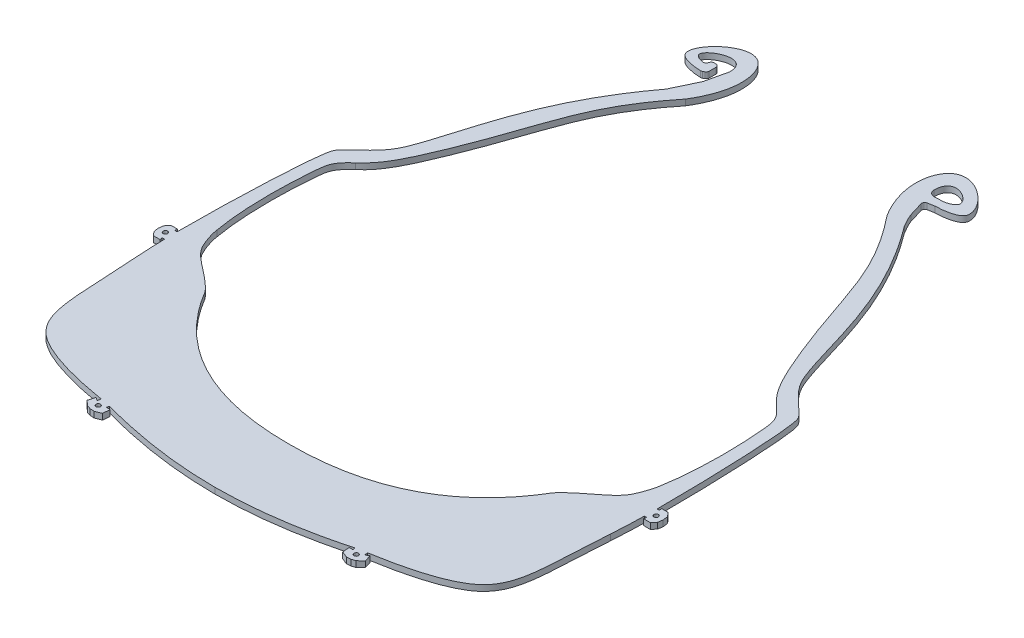
SolidWorks part; units mm, degrees
ref_plane "Front Plane" through (0, 0, 0) normal (0, 0, 1) x (1, 0, 0)
ref_plane "Top Plane" through (0, 0, 0) normal (0, 1, 0) x (1, 0, 0)
ref_plane "Right Plane" through (0, 0, 0) normal (1, 0, 0) x (0, 0, -1)
sketch "Sketch1" plane through (0, 0, 0) normal (0, 1, 0) x (1, 0, 0)
  line L0 (-56.7342, 4649.685) -> (-54.3432, 4649.8666)
  line L1 (-54.3432, 4649.8666) -> (-51.9673, 4650.1279)
  line L2 (-51.9673, 4650.1279) -> (-49.6128, 4650.4904)
  line L3 (-49.6128, 4650.4904) -> (-47.2873, 4650.9763)
  line L4 (-47.2873, 4650.9763) -> (-45.0028, 4651.606)
  line L5 (-45.0028, 4651.606) -> (-42.7754, 4652.393)
  line L6 (-42.7754, 4652.393) -> (-40.6236, 4653.3398)
  line L7 (-40.6236, 4653.3398) -> (-38.5569, 4654.4471)
  line L8 (-38.5569, 4654.4471) -> (-36.5628, 4655.7048)
  line L9 (-36.5628, 4655.7048) -> (-34.628, 4657.0886)
  line L10 (-34.628, 4657.0886) -> (-32.7572, 4658.5809)
  line L11 (-32.7572, 4658.5809) -> (-31.8781, 4659.3559)
  line L12 (-31.8781, 4659.3559) -> (-31.0378, 4660.1663)
  line L13 (-31.0378, 4660.1663) -> (-30.2434, 4661.0133)
  line L14 (-30.2434, 4661.0133) -> (-29.4929, 4661.8977)
  line L15 (-29.4929, 4661.8977) -> (-28.0377, 4663.8002)
  line L16 (-28.0377, 4663.8002) -> (-26.6418, 4665.7643)
  line L17 (-26.6418, 4665.7643) -> (-25.2842, 4667.7433)
  line L18 (-25.2842, 4667.7433) -> (-24.5616, 4668.7671)
  line L19 (-24.5616, 4668.7671) -> (-24.1207, 4669.3049)
  line L20 (-24.1207, 4669.3049) -> (-23.6287, 4669.8041)
  line L21 (-23.6287, 4669.8041) -> (-22.6527, 4670.6453)
  line L22 (-22.6527, 4670.6453) -> (-21.6624, 4671.4168)
  line L23 (-21.6624, 4671.4168) -> (-19.7154, 4672.8766)
  line L24 (-19.7154, 4672.8766) -> (-18.7888, 4673.6051)
  line L25 (-18.7888, 4673.6051) -> (-17.9151, 4674.3646)
  line L26 (-17.9151, 4674.3646) -> (-17.0961, 4675.1711)
  line L27 (-17.0961, 4675.1711) -> (-16.3332, 4676.0235)
  line L28 (-16.3332, 4676.0235) -> (-14.888, 4677.8872)
  line L29 (-14.888, 4677.8872) -> (-14.2651, 4678.8282)
  line L30 (-14.2651, 4678.8282) -> (-13.7395, 4679.8092)
  line L31 (-13.7395, 4679.8092) -> (-13.3157, 4680.8364)
  line L32 (-13.3157, 4680.8364) -> (-12.9921, 4681.9053)
  line L33 (-12.9921, 4681.9053) -> (-12.765, 4683.0137)
  line L34 (-12.765, 4683.0137) -> (-12.6116, 4684.156)
  line L35 (-12.6116, 4684.156) -> (-12.4221, 4686.5439)
  line L36 (-12.4221, 4686.5439) -> (-12.3049, 4688.9547)
  line L37 (-12.3049, 4688.9547) -> (-12.23, 4691.3606)
  line L38 (-12.23, 4691.3606) -> (-12.2173, 4693.7469)
  line L39 (-12.2173, 4693.7469) -> (-12.2979, 4696.128)
  line L40 (-12.2979, 4696.128) -> (-12.4621, 4698.525)
  line L41 (-12.4621, 4698.525) -> (-12.9016, 4703.3562)
  line L42 (-12.9016, 4703.3562) -> (-13.1725, 4705.7323)
  line L43 (-13.1725, 4705.7323) -> (-13.359, 4706.8497)
  line L44 (-13.359, 4706.8497) -> (-13.6464, 4707.8976)
  line L45 (-13.6464, 4707.8976) -> (-13.8331, 4708.3435)
  line L46 (-13.8331, 4708.3435) -> (-14.0727, 4708.7863)
  line L47 (-14.0727, 4708.7863) -> (-14.3603, 4709.2104)
  line L48 (-14.3603, 4709.2104) -> (-14.6922, 4709.6118)
  line L49 (-14.6922, 4709.6118) -> (-15.5352, 4710.4427)
  line L50 (-15.5352, 4710.4427) -> (-16.4733, 4711.2489)
  line L51 (-16.4733, 4711.2489) -> (-18.3969, 4712.8768)
  line L52 (-18.3969, 4712.8768) -> (-19.3317, 4713.7593)
  line L53 (-19.3317, 4713.7593) -> (-19.7964, 4714.2738)
  line L54 (-19.7964, 4714.2738) -> (-20.226, 4714.8564)
  line L55 (-20.226, 4714.8564) -> (-20.8491, 4716.0227)
  line L56 (-20.8491, 4716.0227) -> (-21.3607, 4717.2182)
  line L57 (-21.3607, 4717.2182) -> (-22.2565, 4719.6128)
  line L58 (-22.2565, 4719.6128) -> (-23.9365, 4724.4003)
  line L59 (-23.9365, 4724.4003) -> (-24.8142, 4726.6925)
  line L60 (-24.8142, 4726.6925) -> (-25.7235, 4728.951)
  line L61 (-25.7235, 4728.951) -> (-29.4192, 4737.978)
  line L62 (-29.4192, 4737.978) -> (-31.3112, 4742.476)
  line L63 (-31.3112, 4742.476) -> (-32.3108, 4744.6883)
  line L64 (-32.3108, 4744.6883) -> (-33.3653, 4746.8748)
  line L65 (-33.3653, 4746.8748) -> (-34.484, 4749.0197)
  line L66 (-34.484, 4749.0197) -> (-35.6822, 4751.1089)
  line L67 (-35.6822, 4751.1089) -> (-36.9697, 4753.1376)
  line L68 (-36.9697, 4753.1376) -> (-38.335, 4755.1176)
  line L69 (-38.335, 4755.1176) -> (-39.7566, 4757.0561)
  line L70 (-39.7566, 4757.0561) -> (-41.2239, 4758.9538)
  line L71 (-41.2239, 4758.9538) -> (-44.2837, 4762.6862)
  line L72 (-44.2837, 4762.6862) -> (-45.0093, 4763.5782)
  line L73 (-45.7102, 4766.0333) -> (-45.6003, 4766.895)
  line L74 (-44.3387, 4767.2717) -> (-41.5099, 4763.9631)
  line L75 (-41.5099, 4763.9631) -> (-39.7615, 4761.7893)
  line L76 (-39.7615, 4761.7893) -> (-36.1552, 4757.1077)
  line L77 (-36.1552, 4757.1077) -> (-34.4224, 4754.6956)
  line L78 (-34.4224, 4754.6956) -> (-32.818, 4752.1875)
  line L79 (-32.818, 4752.1875) -> (-31.4001, 4749.5854)
  line L80 (-31.4001, 4749.5854) -> (-30.1172, 4746.945)
  line L81 (-30.1172, 4746.945) -> (-27.7453, 4741.6402)
  line L82 (-27.7453, 4741.6402) -> (-25.4835, 4736.2816)
  line L83 (-25.4835, 4736.2816) -> (-23.2904, 4730.8724)
  line L84 (-23.2904, 4730.8724) -> (-21.1708, 4725.4153)
  line L85 (-21.1708, 4725.4153) -> (-19.1018, 4719.943)
  line L86 (-19.1018, 4719.943) -> (-18.1004, 4717.2034)
  line L87 (-18.1004, 4717.2034) -> (-17.875, 4716.5966)
  line L88 (-17.875, 4716.5966) -> (-17.6236, 4716.1359)
  line L89 (-17.6236, 4716.1359) -> (-17.2675, 4715.7336)
  line L90 (-17.2675, 4715.7336) -> (-16.7845, 4715.2999)
  line L91 (-16.7845, 4715.2999) -> (-14.566, 4713.4273)
  line L92 (-14.566, 4713.4273) -> (-13.4359, 4712.453)
  line L93 (-13.4359, 4712.453) -> (-12.2875, 4711.3506)
  line L94 (-12.2875, 4711.3506) -> (-11.7288, 4710.5494)
  line L95 (-11.7288, 4710.5494) -> (-11.4049, 4709.6505)
  line L96 (-11.4049, 4709.6505) -> (-11.1035, 4708.0976)
  line L97 (-11.1035, 4708.0976) -> (-10.7039, 4705.1867)
  line L98 (-10.7039, 4705.1867) -> (-10.3782, 4702.2301)
  line L99 (-10.3782, 4702.2301) -> (-10.1381, 4699.312)
  line L100 (-10.1381, 4699.312) -> (-9.9526, 4696.4059)
  line L101 (-9.9526, 4696.4059) -> (-9.8234, 4693.4642)
  line L102 (-9.8234, 4693.4642) -> (-9.7818, 4690.5097)
  line L103 (-9.7818, 4690.5097) -> (-9.8395, 4687.5651)
  line L104 (-9.8395, 4687.5651) -> (-10.1467, 4681.8499)
  line L105 (-10.2187, 4680.4106) -> (-10.5778, 4674.8324)
  line L106 (-10.5778, 4674.8324) -> (-10.9255, 4669.1921)
  line L107 (-10.9255, 4669.1921) -> (-11.1085, 4666.3239)
  line L108 (-11.1085, 4666.3239) -> (-11.3672, 4663.3976)
  line L109 (-11.3672, 4663.3976) -> (-11.5954, 4661.8877)
  line L110 (-11.5954, 4661.8877) -> (-11.9481, 4660.3817)
  line L111 (-11.9481, 4660.3817) -> (-12.469, 4658.9063)
  line L112 (-12.469, 4658.9063) -> (-13.1768, 4657.5086)
  line L113 (-13.1768, 4657.5086) -> (-14.0475, 4656.2056)
  line L114 (-14.0475, 4656.2056) -> (-15.0678, 4655.0233)
  line L115 (-15.0678, 4655.0233) -> (-15.6664, 4654.4674)
  line L116 (-15.6664, 4654.4674) -> (-16.3022, 4653.9611)
  line L117 (-16.3022, 4653.9611) -> (-17.6055, 4653.1269)
  line L118 (-17.6055, 4653.1269) -> (-18.9712, 4652.4383)
  line L119 (-18.9712, 4652.4383) -> (-20.3502, 4651.8561)
  line L120 (-20.3502, 4651.8561) -> (-21.7405, 4651.3486)
  line L121 (-21.7405, 4651.3486) -> (-23.1491, 4650.8937)
  line L122 (-23.1491, 4650.8937) -> (-25.9685, 4650.1281)
  line L123 (-25.9685, 4650.1281) -> (-28.8127, 4649.495)
  line L124 (-28.8127, 4649.495) -> (-34.3611, 4648.4388)
  line L125 (-35.7786, 4648.1905) -> (-42.1243, 4647.1501)
  line L126 (-42.1243, 4647.1501) -> (-45.3893, 4646.7207)
  line L127 (-45.3893, 4646.7207) -> (-48.6635, 4646.3827)
  line L128 (-48.6635, 4646.3827) -> (-55.1892, 4645.922)
  line L129 (-55.1892, 4645.922) -> (-61.7354, 4645.5886)
  line L130 (-61.7354, 4645.5886) -> (-63.9666, 4645.5453)
  line L131 (-63.9667, 4649.4865) -> (-59.1315, 4649.5688)
  line L132 (-59.1315, 4649.5688) -> (-56.7342, 4649.685)
  line L133 (-9.7721, 4681.8294) -> (-9.752, 4682.186)
  line L134 (-9.752, 4682.186) -> (-9.3693, 4682.5229)
  line L135 (-9.3693, 4682.5229) -> (-8.649, 4682.4768)
  line L136 (-8.649, 4682.4768) -> (-7.9775, 4681.713)
  line L137 (-7.9775, 4681.713) -> (-8.2411, 4680.2884)
  line L138 (-8.2411, 4680.2884) -> (-9.0059, 4679.6162)
  line L139 (-9.0059, 4679.6162) -> (-9.5491, 4679.6473)
  line L140 (-9.5491, 4679.6473) -> (-9.8867, 4680.0303)
  line L141 (-9.8867, 4680.0303) -> (-9.8664, 4680.3889)
  line L142 (-9.7721, 4681.8294) -> (-9.752, 4682.186)
  line L151 (-34.2991, 4648.0806) -> (-33.9447, 4648.1421)
  line L152 (-33.9447, 4648.1421) -> (-33.5285, 4647.8485)
  line L153 (-33.5285, 4647.8485) -> (-33.4056, 4647.1395)
  line L154 (-33.4056, 4647.1395) -> (-33.9931, 4646.3074)
  line L155 (-33.9931, 4646.3074) -> (-35.4108, 4646.0612)
  line L156 (-35.4108, 4646.0612) -> (-36.2441, 4646.6493)
  line L157 (-36.2441, 4646.6493) -> (-36.3669, 4647.358)
  line L158 (-36.3669, 4647.358) -> (-36.0733, 4647.7743)
  line L159 (-36.0733, 4647.7743) -> (-35.7187, 4647.8357)
  line L160 (-10.1467, 4681.8499) -> (-9.7721, 4681.8294)
  line L161 (-34.3611, 4648.4388) -> (-34.2991, 4648.0806)
  line L162 (-35.7786, 4648.1905) -> (-35.7187, 4647.8357)
  line L163 (-9.8664, 4680.3889) -> (-10.2187, 4680.4106)
  line L165 (-118.1813, 4682.186) -> (-118.5641, 4682.5226)
  line L166 (-118.5641, 4682.5226) -> (-119.2843, 4682.4768)
  line L167 (-119.2843, 4682.4768) -> (-119.9558, 4681.7128)
  line L168 (-119.9558, 4681.7128) -> (-119.8643, 4680.2786)
  line L169 (-119.8643, 4680.2786) -> (-119.0995, 4679.6064)
  line L170 (-119.0995, 4679.6064) -> (-118.3843, 4679.6471)
  line L171 (-118.3843, 4679.6471) -> (-118.0466, 4680.0303)
  line L172 (-118.0466, 4680.0303) -> (-118.0672, 4680.3889)
  line L173 (-118.0672, 4680.3889) -> (-117.7148, 4680.4103)
  line L174 (-117.7148, 4680.4103) -> (-117.3555, 4674.8322)
  line L175 (-117.3555, 4674.8322) -> (-117.0078, 4669.1921)
  line L176 (-117.0078, 4669.1921) -> (-116.8249, 4666.3237)
  line L177 (-116.8249, 4666.3237) -> (-116.566, 4663.3974)
  line L178 (-116.566, 4663.3974) -> (-116.3378, 4661.8875)
  line L179 (-116.3378, 4661.8875) -> (-115.9851, 4660.3817)
  line L180 (-115.9851, 4660.3817) -> (-115.4645, 4658.906)
  line L181 (-115.4645, 4658.906) -> (-114.7563, 4657.5086)
  line L182 (-114.7563, 4657.5086) -> (-113.8857, 4656.2053)
  line L183 (-113.8857, 4656.2053) -> (-112.8656, 4655.0233)
  line L184 (-112.8656, 4655.0233) -> (-112.2669, 4654.4674)
  line L185 (-112.2669, 4654.4674) -> (-111.6311, 4653.9608)
  line L186 (-111.6311, 4653.9608) -> (-110.328, 4653.1269)
  line L187 (-110.328, 4653.1269) -> (-108.9621, 4652.4383)
  line L188 (-108.9621, 4652.4383) -> (-107.5832, 4651.8561)
  line L189 (-107.5832, 4651.8561) -> (-106.1928, 4651.3484)
  line L190 (-106.1928, 4651.3484) -> (-104.7844, 4650.8937)
  line L191 (-104.7844, 4650.8937) -> (-101.9649, 4650.1279)
  line L192 (-101.9649, 4650.1279) -> (-99.1205, 4649.4948)
  line L193 (-99.1205, 4649.4948) -> (-93.5721, 4648.4388)
  line L194 (-93.5721, 4648.4388) -> (-93.6341, 4648.0806)
  line L195 (-93.6341, 4648.0806) -> (-93.9885, 4648.1421)
  line L196 (-93.9885, 4648.1421) -> (-94.4046, 4647.8485)
  line L197 (-94.4046, 4647.8485) -> (-94.5276, 4647.1392)
  line L198 (-94.5276, 4647.1392) -> (-93.9404, 4646.3074)
  line L199 (-93.9404, 4646.3074) -> (-92.5223, 4646.0612)
  line L200 (-92.5223, 4646.0612) -> (-91.6891, 4646.6493)
  line L201 (-91.6891, 4646.6493) -> (-91.5662, 4647.358)
  line L202 (-91.5662, 4647.358) -> (-91.8598, 4647.7743)
  line L203 (-91.8598, 4647.7743) -> (-92.2145, 4647.8357)
  line L204 (-92.1546, 4648.1905) -> (-92.2145, 4647.8357)
  line L205 (-92.1546, 4648.1905) -> (-85.8089, 4647.1501)
  line L206 (-85.8089, 4647.1501) -> (-82.5441, 4646.7204)
  line L207 (-82.5441, 4646.7204) -> (-79.2698, 4646.3827)
  line L208 (-79.2698, 4646.3827) -> (-72.7439, 4645.922)
  line L209 (-72.7439, 4645.922) -> (-66.1978, 4645.5886)
  line L210 (-66.1978, 4645.5886) -> (-63.9666, 4645.5453)
  line L211 (-63.9667, 4649.4865) -> (-68.8018, 4649.5688)
  line L212 (-68.8018, 4649.5688) -> (-71.1991, 4649.685)
  line L213 (-71.1991, 4649.685) -> (-73.5901, 4649.8666)
  line L214 (-73.5901, 4649.8666) -> (-75.9659, 4650.1279)
  line L215 (-75.9659, 4650.1279) -> (-78.3204, 4650.4904)
  line L216 (-78.3204, 4650.4904) -> (-80.646, 4650.976)
  line L217 (-80.646, 4650.976) -> (-82.9304, 4651.606)
  line L218 (-82.9304, 4651.606) -> (-85.1578, 4652.393)
  line L219 (-85.1578, 4652.393) -> (-87.3097, 4653.3398)
  line L220 (-87.3097, 4653.3398) -> (-89.3762, 4654.4469)
  line L221 (-89.3762, 4654.4469) -> (-91.3704, 4655.7045)
  line L222 (-91.3704, 4655.7045) -> (-93.3054, 4657.0883)
  line L223 (-93.3054, 4657.0883) -> (-95.1761, 4658.5809)
  line L224 (-95.1761, 4658.5809) -> (-96.0551, 4659.3559)
  line L225 (-96.0551, 4659.3559) -> (-96.8955, 4660.1661)
  line L226 (-96.8955, 4660.1661) -> (-97.6899, 4661.013)
  line L227 (-97.6899, 4661.013) -> (-98.4405, 4661.8974)
  line L228 (-98.4405, 4661.8974) -> (-99.8956, 4663.8003)
  line L229 (-99.8956, 4663.8003) -> (-101.2917, 4665.7643)
  line L230 (-101.2917, 4665.7643) -> (-102.649, 4667.7433)
  line L231 (-102.649, 4667.7433) -> (-103.3717, 4668.7671)
  line L232 (-103.3717, 4668.7671) -> (-103.8126, 4669.3049)
  line L233 (-103.8126, 4669.3049) -> (-104.3045, 4669.8038)
  line L234 (-104.3045, 4669.8038) -> (-105.2805, 4670.645)
  line L235 (-105.2805, 4670.645) -> (-106.2711, 4671.4168)
  line L236 (-106.2711, 4671.4168) -> (-108.218, 4672.8766)
  line L237 (-108.218, 4672.8766) -> (-109.1446, 4673.6051)
  line L238 (-109.1446, 4673.6051) -> (-110.0184, 4674.3646)
  line L239 (-110.0184, 4674.3646) -> (-110.8371, 4675.1711)
  line L240 (-110.8371, 4675.1711) -> (-111.6001, 4676.0232)
  line L241 (-111.6001, 4676.0232) -> (-113.0454, 4677.8872)
  line L242 (-113.0454, 4677.8872) -> (-113.6683, 4678.8282)
  line L243 (-113.6683, 4678.8282) -> (-114.1938, 4679.8092)
  line L244 (-114.1938, 4679.8092) -> (-114.6176, 4680.8364)
  line L245 (-114.6176, 4680.8364) -> (-114.9413, 4681.905)
  line L246 (-114.9413, 4681.905) -> (-115.1684, 4683.0135)
  line L247 (-115.1684, 4683.0135) -> (-115.3218, 4684.156)
  line L248 (-115.3218, 4684.156) -> (-115.5115, 4686.5436)
  line L249 (-115.5115, 4686.5436) -> (-115.6283, 4688.9545)
  line L250 (-115.6283, 4688.9545) -> (-115.7033, 4691.3606)
  line L251 (-115.7033, 4691.3606) -> (-115.7161, 4693.7466)
  line L252 (-115.7161, 4693.7466) -> (-115.6355, 4696.1278)
  line L253 (-115.6355, 4696.1278) -> (-115.4714, 4698.525)
  line L254 (-115.4714, 4698.525) -> (-115.0316, 4703.3562)
  line L255 (-115.0316, 4703.3562) -> (-114.7608, 4705.732)
  line L256 (-114.7608, 4705.732) -> (-114.5743, 4706.8497)
  line L257 (-114.5743, 4706.8497) -> (-114.287, 4707.8977)
  line L258 (-114.287, 4707.8977) -> (-114.1002, 4708.3435)
  line L259 (-114.1002, 4708.3435) -> (-113.8608, 4708.7862)
  line L260 (-113.8608, 4708.7862) -> (-113.5731, 4709.2103)
  line L261 (-113.5731, 4709.2103) -> (-113.2411, 4709.6117)
  line L262 (-113.2411, 4709.6117) -> (-112.3981, 4710.4425)
  line L263 (-112.3981, 4710.4425) -> (-111.4599, 4711.2487)
  line L264 (-111.4599, 4711.2487) -> (-109.5364, 4712.8767)
  line L265 (-109.5364, 4712.8767) -> (-108.602, 4713.7592)
  line L266 (-108.602, 4713.7592) -> (-108.1369, 4714.2737)
  line L267 (-108.1369, 4714.2737) -> (-107.7072, 4714.8564)
  line L268 (-107.7072, 4714.8564) -> (-107.0842, 4716.0225)
  line L269 (-107.0842, 4716.0225) -> (-106.5727, 4717.2181)
  line L270 (-106.5727, 4717.2181) -> (-105.6769, 4719.6127)
  line L271 (-105.6769, 4719.6127) -> (-103.9969, 4724.4001)
  line L272 (-103.9969, 4724.4001) -> (-103.1193, 4726.6924)
  line L273 (-103.1193, 4726.6924) -> (-102.2099, 4728.9509)
  line L274 (-102.2099, 4728.9509) -> (-98.5143, 4737.9778)
  line L275 (-98.5143, 4737.9778) -> (-96.6221, 4742.4757)
  line L276 (-96.6221, 4742.4757) -> (-95.6227, 4744.6884)
  line L277 (-95.6227, 4744.6884) -> (-94.5682, 4746.8748)
  line L278 (-94.5682, 4746.8748) -> (-93.4493, 4749.0197)
  line L279 (-93.4493, 4749.0197) -> (-92.2515, 4751.1088)
  line L280 (-92.2515, 4751.1088) -> (-90.9637, 4753.1374)
  line L281 (-90.9637, 4753.1374) -> (-89.5985, 4755.1174)
  line L282 (-89.5985, 4755.1174) -> (-88.177, 4757.0561)
  line L283 (-88.177, 4757.0561) -> (-86.7094, 4758.9538)
  line L284 (-86.7094, 4758.9538) -> (-83.65, 4762.6862)
  line L285 (-83.65, 4762.6862) -> (-82.924, 4763.5782)
  line L286 (-82.2232, 4766.0334) -> (-82.3333, 4766.8949)
  line L287 (-83.5948, 4767.2716) -> (-86.4235, 4763.963)
  line L288 (-86.4235, 4763.963) -> (-88.172, 4761.7894)
  line L289 (-88.172, 4761.7894) -> (-91.7784, 4757.1074)
  line L290 (-91.7784, 4757.1074) -> (-93.5112, 4754.6958)
  line L291 (-93.5112, 4754.6958) -> (-95.1154, 4752.1875)
  line L292 (-95.1154, 4752.1875) -> (-96.5333, 4749.5852)
  line L293 (-96.5333, 4749.5852) -> (-97.8162, 4746.9449)
  line L294 (-97.8162, 4746.9449) -> (-100.1881, 4741.6403)
  line L295 (-100.1881, 4741.6403) -> (-102.4501, 4736.2814)
  line L296 (-102.4501, 4736.2814) -> (-104.6429, 4730.8726)
  line L297 (-104.6429, 4730.8726) -> (-106.7626, 4725.415)
  line L298 (-106.7626, 4725.415) -> (-108.8314, 4719.9429)
  line L299 (-108.8314, 4719.9429) -> (-109.8329, 4717.2035)
  line L300 (-109.8329, 4717.2035) -> (-110.0583, 4716.5964)
  line L301 (-110.0583, 4716.5964) -> (-110.3097, 4716.1357)
  line L302 (-110.3097, 4716.1357) -> (-110.6661, 4715.7335)
  line L303 (-110.6661, 4715.7335) -> (-111.1489, 4715.2998)
  line L304 (-111.1489, 4715.2998) -> (-113.3676, 4713.4272)
  line L305 (-113.3676, 4713.4272) -> (-114.4976, 4712.4528)
  line L306 (-114.4976, 4712.4528) -> (-115.646, 4711.3505)
  line L307 (-115.646, 4711.3505) -> (-116.2044, 4710.5493)
  line L308 (-116.2044, 4710.5493) -> (-116.5286, 4709.6504)
  line L309 (-116.5286, 4709.6504) -> (-116.8298, 4708.0975)
  line L310 (-116.8298, 4708.0975) -> (-117.2296, 4705.1868)
  line L311 (-117.2296, 4705.1868) -> (-117.5553, 4702.2301)
  line L312 (-117.5553, 4702.2301) -> (-117.7952, 4699.312)
  line L313 (-117.7952, 4699.312) -> (-117.981, 4696.4059)
  line L314 (-117.981, 4696.4059) -> (-118.11, 4693.4642)
  line L315 (-118.11, 4693.4642) -> (-118.1516, 4690.5097)
  line L316 (-118.1516, 4690.5097) -> (-118.0939, 4687.5649)
  line L317 (-118.0939, 4687.5649) -> (-117.7865, 4681.8497)
  line L318 (-117.7865, 4681.8497) -> (-118.1612, 4681.8294)
  line L319 (-118.1612, 4681.8294) -> (-118.1813, 4682.186)
  spline S0 degree 3 poles (-45.7102, 4766.0333) (-45.8224, 4765.1537) (-45.5692, 4764.2663) (-45.0093, 4763.5782) knots 0 0 0 0 1 1 1 1
  spline S1 degree 3 poles (-44.3387, 4767.2717) (-44.5973, 4767.574) (-45.0517, 4767.6095) (-45.3539, 4767.351) knots 0 0 0 0 1 1 1 1
  spline S2 degree 3 poles (-45.3539, 4767.351) (-45.4898, 4767.2349) (-45.5777, 4767.0723) (-45.6003, 4766.895) knots 0 0 0 0 1 1 1 1
  spline S3 degree 3 poles (-82.924, 4763.5782) (-82.3642, 4764.2661) (-82.111, 4765.1536) (-82.2232, 4766.0334) knots 0 0 0 0 1 1 1 1
  spline S4 degree 3 poles (-82.3333, 4766.8949) (-82.3835, 4767.2894) (-82.7441, 4767.5683) (-83.1386, 4767.518) knots 0 0 0 0 1 1 1 1
  spline S5 degree 3 poles (-83.1386, 4767.518) (-83.3159, 4767.4954) (-83.4785, 4767.4075) (-83.5948, 4767.2716) knots 0 0 0 0 1 1 1 1
sketch "Sketch2" plane through (0, 0, 0) normal (0, 1, 0) x (1, 0, 0)
  line L0 (-63.9234, 4631.4262) -> (-63.9234, 4609.4594) construction
  line L25 (-22.4985, 4637.3551) -> (-18.9434, 4638.0357) construction
  line L26 (-20.7209, 4637.6954) -> (-20.3316, 4635.6618) construction
  line L31 (-16.9423, 4635.297) -> (-18.5347, 4633.796)
  line L32 (-20.3316, 4635.6618) -> (-19.8467, 4633.1287) construction
  line L33 (-18.5347, 4633.796) -> (-19.8873, 4633.3404)
  line L34 (-21.3125, 4633.2642) -> (-19.8873, 4633.3404)
  line L35 (-23.3466, 4634.071) -> (-21.3125, 4633.2642)
  line L49 (-146.8202, 4697.6298) -> (-149.3915, 4697.5949) construction
  line L50 (16.9036, 4697.658) -> (18.9735, 4697.6298) construction
  line L54 (20.0716, 4700.6062) -> (21.1812, 4699.2558)
  line L55 (18.9735, 4697.6298) -> (21.5448, 4697.5949) construction
  line L56 (21.1812, 4699.2558) -> (21.376, 4697.5972)
  line L57 (21.1362, 4695.9445) -> (21.376, 4697.5972)
  line L58 (19.9903, 4694.6247) -> (21.1362, 4695.9445)
  line L62 (-144.7504, 4697.658) -> (-146.8202, 4697.6298) construction
  line L73 (17.8327, 4700.6671) -> (20.0716, 4700.6062)
  line L74 (17.7506, 4694.6247) -> (19.9903, 4694.6247)
  line L75 (-23.5736, 4636.4725) -> (-23.3466, 4634.071)
  line L76 (-17.6183, 4637.6126) -> (-16.9423, 4635.297)
  line L77 (-26.6214, 4837.9355) -> (-27.2964, 4837.8992)
  line L78 (-24.4559, 4835.3139) -> (-26.7647, 4834.9076)
  line L87 (-23.5736, 4636.4725) -> (-22.2692, 4636.4725)
  line L88 (-22.2692, 4636.4725) -> (-22.4985, 4637.3551)
  line L89 (-17.6183, 4637.6126) -> (-18.7357, 4636.9369)
  line L90 (-18.7357, 4636.9369) -> (-18.9434, 4638.0357)
  line L91 (17.093, 4695.5191) -> (17.927, 4695.5191)
  line L92 (17.927, 4695.5191) -> (17.7506, 4694.6247)
  line L93 (17.151, 4699.7908) -> (17.9273, 4699.7908)
  line L94 (17.9273, 4699.7908) -> (17.8327, 4700.6671)
  line L98 (-63.9234, 4656.5726) -> (-63.9234, 4631.4262) construction
  line L99 (-107.5151, 4635.6618) -> (-108, 4633.1287) construction
  line L100 (-107.1258, 4637.6954) -> (-107.5151, 4635.6618) construction
  line L101 (-105.3482, 4637.3551) -> (-108.9034, 4638.0357) construction
  line L102 (-145.774, 4699.7908) -> (-145.6794, 4700.6671)
  line L103 (-144.9978, 4699.7908) -> (-145.774, 4699.7908)
  line L104 (-145.7738, 4695.5191) -> (-145.5973, 4694.6247)
  line L105 (-144.9397, 4695.5191) -> (-145.7738, 4695.5191)
  line L106 (-109.111, 4636.9369) -> (-108.9034, 4638.0357)
  line L107 (-110.2284, 4637.6126) -> (-109.111, 4636.9369)
  line L108 (-105.5775, 4636.4725) -> (-105.3482, 4637.3551)
  line L109 (-104.2732, 4636.4725) -> (-105.5775, 4636.4725)
  line L112 (-110.2284, 4637.6126) -> (-110.9044, 4635.297)
  line L113 (-104.2732, 4636.4725) -> (-104.5002, 4634.071)
  line L114 (-145.5973, 4694.6247) -> (-147.8371, 4694.6247)
  line L115 (-145.6794, 4700.6671) -> (-147.9184, 4700.6062)
  line L116 (-147.8371, 4694.6247) -> (-148.983, 4695.9445)
  line L117 (-148.983, 4695.9445) -> (-149.2228, 4697.5972)
  line L118 (-149.028, 4699.2558) -> (-149.2228, 4697.5972)
  line L119 (-147.9184, 4700.6062) -> (-149.028, 4699.2558)
  line L120 (-104.5002, 4634.071) -> (-106.5343, 4633.2642)
  line L121 (-106.5343, 4633.2642) -> (-107.9595, 4633.3404)
  line L122 (-109.3121, 4633.796) -> (-107.9595, 4633.3404)
  line L123 (-110.9044, 4635.297) -> (-109.3121, 4633.796)
  line L124 (-98.4431, 4839.9128) -> (-100.1349, 4832.5304)
  line L125 (-104.1397, 4824.1329) -> (-100.1349, 4832.5304)
  line L126 (-104.7915, 4838.8777) -> (-104.6455, 4839.2653)
  line L127 (-103.7097, 4839.9128) -> (-103.103, 4839.9128)
  line L128 (-102.103, 4838.9128) -> (-102.103, 4836.6309)
  line L129 (-102.6062, 4835.7631) -> (-103.1569, 4835.4478)
  line L130 (-26.0413, 4828.6569) -> (-27.5485, 4833.6329)
  circle A0 centre (28.2666, 4698.0399) radius 0.5
  circle A1 centre (-20.3316, 4635.6618) radius 0.75
  circle A4 centre (18.9735, 4697.6298) radius 0.75
  arc A7 (-29.4037, 4839.9128) -> (-27.2964, 4837.8992) centre (-27.4037, 4839.8963) ccw
  circle A10 centre (-146.8202, 4697.6298) radius 0.75
  circle A11 centre (-107.5151, 4635.6618) radius 0.75
  circle A12 centre (-156.1134, 4698.0399) radius 0.5
  arc A14 (-103.668, 4835.3158) -> (-103.1569, 4835.4478) centre (-103.6537, 4836.3157) ccw
  arc A15 (-104.7915, 4838.8777) -> (-105.901, 4838.2454) centre (-105.7273, 4839.2302) cw
  arc A16 (-104.6455, 4839.2653) -> (-103.7097, 4839.9128) centre (-103.7097, 4838.9128) cw
  arc A17 (-103.103, 4839.9128) -> (-102.103, 4838.9128) centre (-103.103, 4838.9128) cw
  arc A18 (-102.103, 4836.6309) -> (-102.6062, 4835.7631) centre (-103.103, 4836.6309) cw
  arc A19 (-27.5485, 4833.6329) -> (-26.7647, 4834.9076) centre (-26.5914, 4833.9227) cw
  spline S0 degree 3 poles (-63.9234, 4631.4262) (-49.9972, 4631.4534) (-36.075, 4633.5591) (-22.4985, 4637.3551) knots 0.500293 0.500293 0.500293 0.500293 0.981945 0.981945 0.981945 0.981945
  spline S1 degree 3 poles (-18.9434, 4638.0357) (-9.0248, 4639.6859) (4.6467, 4643.0604) (16.372, 4654.3944) (15.2524, 4666.3346) (16.6172, 4684.5147) knots 0.018902 0.018902 0.018902 0.018902 0.394122 0.490995 0.987629 0.987629 0.987629 0.987629
  spline S2 degree 3 poles (16.6172, 4684.5147) (16.7593, 4687.5885) (17.0552, 4691.3248) (17.093, 4695.5191) knots 0.004735 0.004735 0.004735 0.004735 0.035162 0.035162 0.035162 0.035162
  spline S3 degree 3 poles (17.151, 4699.7908) (17.187, 4718.7532) (15.9465, 4748.1487) (12.9959, 4752.2098) (5.5963, 4758.139) (-2.1217, 4776.0767) (-5.0929, 4799.3689) (-23.7071, 4824.1329) knots 0.04445 0.04445 0.04445 0.04445 0.175223 0.204985 0.326837 0.407861 1 1 1 1
  spline S4 degree 2 poles (-63.9234, 4656.5726) (-23.3221, 4656.4521) (-5.293, 4686.6697) knots 0 0 0 1 1 1
  spline S5 degree 3 poles (-5.293, 4686.6697) (-3.3882, 4689.5147) (5.5322, 4695.6316) (7.0158, 4697.627) (8.9185, 4699.9572) (10.6489, 4704.6448) (10.9298, 4707.0618) knots 0 0 0 0 0.517385 0.711984 0.762678 1 1 1 1
  spline S6 degree 3 poles (10.9298, 4707.0618) (12.5257, 4715.666) (12.951, 4730.9053) (11.2091, 4746.2487) (8.6834, 4748.7091) (7.186, 4750.111) knots 0 0 0 0 0.7977 0.8977 1 1 1 1
  spline S7 degree 3 poles (7.186, 4750.111) (2.6584, 4753.9043) (-14.7649, 4791.2853) (-13.1871, 4803.6512) (-29.8753, 4824.4789) knots 0 0 0 0 0.147118 0.925748 0.925748 0.925748 0.925748
  spline S8 degree 3 poles (-23.7071, 4824.1329) (-24.6028, 4825.7526) (-25.237, 4826.6462) (-26.0413, 4828.6569) knots 0 0 0 0 0.008449 0.008449 0.008449 0.008449
  spline S9 degree 3 poles (-103.668, 4835.3158) (-106.3943, 4835.3548) (-110.9581, 4836.3182) (-112.8542, 4842.5294) (-95.4282, 4857.5196) (-90.9317, 4835.7845) (-97.9715, 4824.4789) knots 0.331986 0.331986 0.331986 0.331986 0.418389 0.461524 0.763332 1 1 1 1
  spline S10 degree 3 poles (-98.4431, 4839.9128) (-98.4489, 4840.6178) (-99.4378, 4847.665) (-110.9591, 4841.3586) (-107.7803, 4838.7055) (-106.6243, 4838.373) (-105.901, 4838.2454) knots 0.039445 0.039445 0.039445 0.039445 0.048335 0.142928 0.155381 0.172867 0.172867 0.172867 0.172867
  spline S12 degree 3 poles (-135.0327, 4750.111) (-130.5051, 4753.9043) (-113.0819, 4791.2853) (-114.6597, 4803.6512) (-97.9715, 4824.4789) knots 0 0 0 0 0.147118 0.925748 0.925748 0.925748 0.925748
  spline S13 degree 3 poles (-138.7766, 4707.0618) (-140.3724, 4715.666) (-140.7978, 4730.9053) (-139.0558, 4746.2487) (-136.5302, 4748.7091) (-135.0327, 4750.111) knots 0 0 0 0 0.7977 0.8977 1 1 1 1
  spline S14 degree 3 poles (-122.5537, 4686.6697) (-124.4586, 4689.5147) (-133.3789, 4695.6316) (-134.8625, 4697.627) (-136.7653, 4699.9572) (-138.4957, 4704.6448) (-138.7766, 4707.0618) knots 0 0 0 0 0.517385 0.711984 0.762678 1 1 1 1
  spline S15 degree 2 poles (-63.9234, 4656.5726) (-104.5246, 4656.4521) (-122.5537, 4686.6697) knots 0 0 0 1 1 1
  spline S16 degree 3 poles (-29.4037, 4839.9128) (-29.3978, 4840.6178) (-28.3384, 4847.6676) (-18.26, 4841.0874) (-23.5487, 4837.8313) (-24.8267, 4838.032) (-26.6214, 4837.9355) knots 0.039445 0.039445 0.039445 0.039445 0.048335 0.142928 0.159173 0.210778 0.210778 0.210778 0.210778
  spline S17 degree 3 poles (-24.4559, 4835.3139) (-21.6711, 4835.3115) (-16.9093, 4836.2726) (-14.9723, 4842.5215) (-32.4226, 4857.5197) (-36.9151, 4835.7845) (-29.8753, 4824.4789) knots 0.329046 0.329046 0.329046 0.329046 0.418095 0.461524 0.763332 1 1 1 1
  spline S18 degree 3 poles (-144.9978, 4699.7908) (-145.0338, 4718.7532) (-143.7933, 4748.1487) (-140.8427, 4752.2098) (-133.443, 4758.139) (-125.725, 4776.0767) (-122.7539, 4799.3689) (-104.1397, 4824.1329) knots 0.04445 0.04445 0.04445 0.04445 0.175223 0.204985 0.326837 0.407861 1 1 1 1
  spline S19 degree 3 poles (-144.464, 4684.5147) (-144.6061, 4687.5885) (-144.9019, 4691.3248) (-144.9397, 4695.5191) knots 0.004735 0.004735 0.004735 0.004735 0.035162 0.035162 0.035162 0.035162
  spline S20 degree 3 poles (-108.9034, 4638.0357) (-118.822, 4639.6859) (-132.4935, 4643.0604) (-144.2188, 4654.3944) (-143.0991, 4666.3346) (-144.464, 4684.5147) knots 0.018902 0.018902 0.018902 0.018902 0.394122 0.490995 0.987629 0.987629 0.987629 0.987629
  spline S21 degree 3 poles (-63.9234, 4631.4262) (-77.8496, 4631.4534) (-91.7718, 4633.5591) (-105.3482, 4637.3551) knots 0.500293 0.500293 0.500293 0.500293 0.981945 0.981945 0.981945 0.981945
  dimension "D1" = 1
  dimension "D2" = 1
  dimension "D3" = 1
extrude "Boss-Extrude2" add sketch "Sketch2" along normal blind 2 separate body
